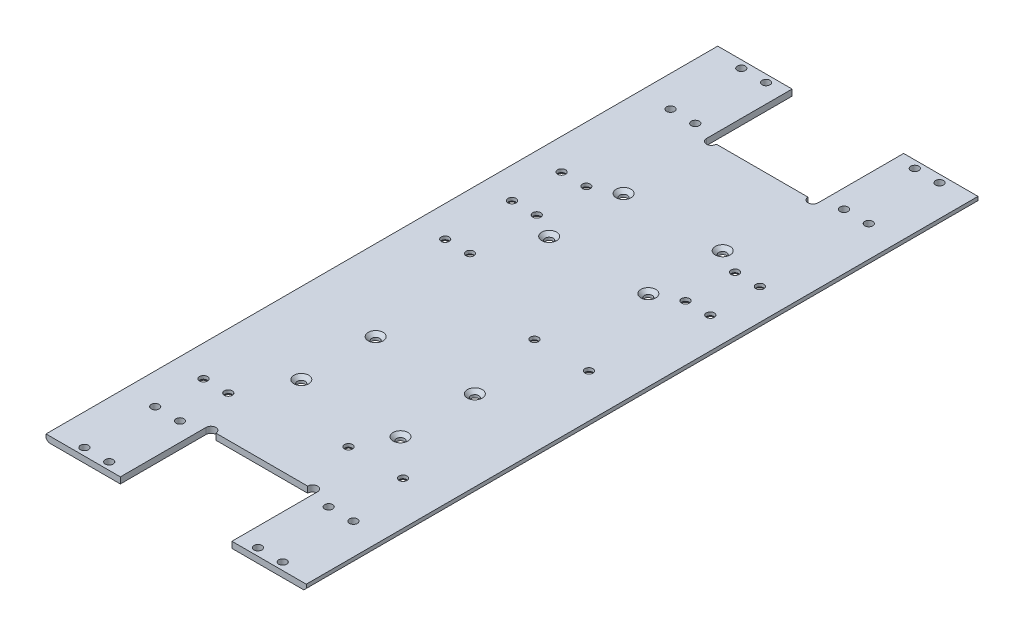
SolidWorks part; units mm, degrees
material "Thornel Mat VMA"
ref_plane "前视基准面" through (0, 0, 0) normal (0, 0, 1) x (1, 0, 0)
ref_plane "上视基准面" through (0, 0, 0) normal (0, 1, 0) x (1, 0, 0)
ref_plane "右视基准面" through (0, 0, 0) normal (1, 0, 0) x (0, 0, -1)
sketch "草图1" plane through (0, 0, 0) normal (0, 1, 0) x (1, 0, 0)
  line L6 (-52.5, -135.5) -> (52.5, -135.5)
  line L7 (52.5, -135.5) -> (52.5, 135.5)
  line L8 (-52.5, 135.5) -> (52.5, 135.5)
  line L9 (-52.5, -135.5) -> (-52.5, 135.5)
  point P8 (-50, 0)
extrude "凸台-拉伸1" add sketch "草图1" along normal blind 2.5
sketch "草图2" plane through (0, 2.5, 0) normal (0, 1, 0) x (1, 0, 0)
  circle A14 centre (35, -3.95) radius 1.6
  circle A15 centre (13, -3.95) radius 1.6
  circle A18 centre (35, -78.95) radius 1.6
  circle A19 centre (13, -78.95) radius 1.6
  circle A32 centre (20, -35) radius 1.6
  circle A33 centre (-20, -35) radius 1.6
  circle A34 centre (20, -65) radius 1.6
  circle A35 centre (-20, -65) radius 1.6
  circle A36 centre (-20, 35) radius 1.6
  circle A37 centre (20, 35) radius 1.6
  circle A40 centre (-20, 65) radius 1.6
  circle A41 centre (20, 65) radius 1.6
extrude "切除-拉伸1" cut sketch "草图2" against normal blind 10
sketch "草图7" plane through (0, 2.5, 0) normal (0, 1, 0) x (1, 0, 0)
  line L0 (0, -1.375) -> (0, 1.375) construction
  circle A0 centre (-40, 60) radius 1.6
  circle A1 centre (-30, 60) radius 1.6
  circle A2 centre (30, 60) radius 1.6
  circle A3 centre (40, 60) radius 1.6
  circle A4 centre (-40, 40) radius 1.6
  circle A5 centre (-30, 40) radius 1.6
  circle A6 centre (30, 40) radius 1.6
  circle A7 centre (40, 40) radius 1.6
  dimension "D1" = 2
chamfer "倒角4" distance 1.4 angle 45 8 edges at (-20, 2.5, 63.4) (-20, 2.5, 33.4) (20, 2.5, 66.6) (20, 2.5, 36.6) (-20, 2.5, -33.4) (-20, 2.5, -63.4) (20, 2.5, -36.6) (20, 2.5, -66.6)
chamfer "倒角5" distance 1 angle 45 2 edges at (52.5, 0, 0) (-52.5, 0, 0)
sketch "草图4" plane through (0, 0, 0) normal (0, -1, 0) x (1, 0, 0)
  line L0 (1.375, 0) -> (-1.375, 0) construction
  line L1 (-51.5, 135.5) -> (51.5, 135.5) construction
  line L2 (0, 100.95) -> (22.5, 100.95)
  line L3 (22.5, 100.95) -> (22.5, 135.5)
  line L4 (22.5, 135.5) -> (-22.5, 135.5)
  line L5 (-22.5, 135.5) -> (-22.5, 100.95)
  line L6 (-22.5, 100.95) -> (0, 100.95)
  line L7 (-22.5, -100.95) -> (0, -100.95)
  line L8 (-22.5, -135.5) -> (-22.5, -100.95)
  line L9 (22.5, -135.5) -> (-22.5, -135.5)
  line L10 (22.5, -100.95) -> (22.5, -135.5)
  line L11 (0, -100.95) -> (22.5, -100.95)
extrude "切除-拉伸2" cut sketch "草图4" against normal blind 10
sketch "草图6" plane through (0, 0, 0) normal (0, -1, 0) x (1, 0, 0)
  line L0 (0, -1.375) -> (0, 1.375) construction
  line L2 (1.375, 0) -> (-1.375, 0) construction
  circle A0 centre (-40, 132.5) radius 1.6
  circle A1 centre (-30, 132.5) radius 1.6
  circle A2 centre (-30, 103.95) radius 1.6
  circle A3 centre (-40, 103.95) radius 1.6
  circle A4 centre (40, 103.95) radius 1.6
  circle A5 centre (30, 103.95) radius 1.6
  circle A6 centre (30, 132.5) radius 1.6
  circle A7 centre (40, 132.5) radius 1.6
  circle A8 centre (40, -132.5) radius 1.6
  circle A9 centre (30, -132.5) radius 1.6
  circle A10 centre (30, -103.95) radius 1.6
  circle A11 centre (40, -103.95) radius 1.6
  circle A12 centre (-40, -103.95) radius 1.6
  circle A13 centre (-30, -103.95) radius 1.6
  circle A14 centre (-30, -132.5) radius 1.6
  circle A15 centre (-40, -132.5) radius 1.6
extrude "切除-拉伸3" cut sketch "草图6" against normal blind 10
extrude "切除-拉伸4" cut sketch "草图7" against normal blind 10
sketch "草图8" plane through (0, 0, 0) normal (0, -1, 0) x (1, 0, 0)
  line L4 (-40, 132.5) -> (-30, 132.5)
  circle A1 centre (-40, 84.45) radius 1.6
  circle A2 centre (-30, 84.45) radius 1.6
  circle A3 centre (-40, -13.05) radius 1.6
  circle A4 centre (-30, -13.05) radius 1.6
extrude "切除-拉伸5" cut sketch "草图8" against normal blind 10 contours A1 | A2 | A4 | A3
sketch "草图9" plane through (0, 0, 0) normal (0, -1, 0) x (1, 0, 0)
  line L0 (0, -1.375) -> (0, 1.375) construction
  line L1 (1.375, 0) -> (-1.375, 0) construction
  line L2 (-22.5, 100.95) -> (22.5, 100.95) construction
  circle A3 centre (20.5, 100.95) radius 2
  circle A4 centre (-20.5, 100.95) radius 2
  circle A5 centre (-20.5, -100.95) radius 2
  circle A6 centre (20.5, -100.95) radius 2
extrude "切除-拉伸6" cut sketch "草图9" against normal blind 10
chamfer "倒角3" distance 1.2 angle 45 16 edges at (13, 0, 2.35) (35, 0, 2.35) (35, 0, 77.35) (13, 0, 77.35) (40, 0, -61.6) (30, 0, -61.6) (-30, 0, -61.6) (-40, 0, -61.6) (-30, 0, -14.65) (-40, 0, -14.65) (-30, 0, 82.85) (-40, 0, 82.85) (-40, 0, -41.6) (-30, 0, -41.6) (30, 0, -41.6) (40, 0, -41.6)
